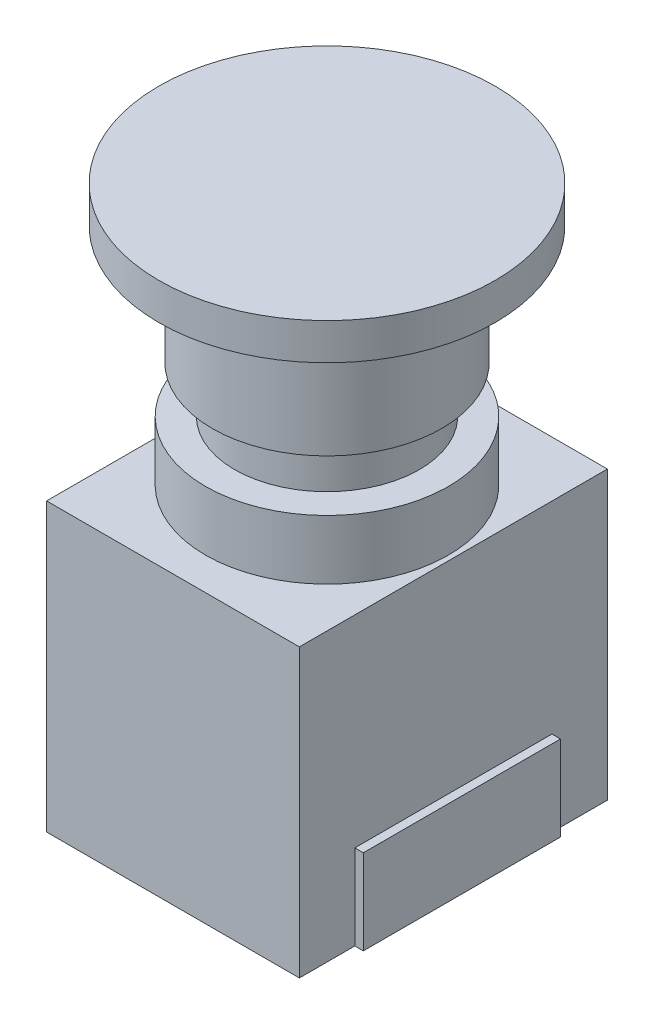
SolidWorks part; units mm, degrees
ref_plane "Front Plane" through (0, 0, 0) normal (0, 0, 1) x (1, 0, 0)
ref_plane "Top Plane" through (0, 0, 0) normal (0, 1, 0) x (1, 0, 0)
ref_plane "Right Plane" through (0, 0, 0) normal (1, 0, 0) x (0, 0, -1)
sketch "Sketch2" plane through (0, 0, 0) normal (0, 1, 0) x (1, 0, 0)
  line L1 (14.875, -18.125) -> (-14.875, -18.125)
  line L2 (14.875, -18.125) -> (14.875, 18.125)
  line L3 (14.875, 18.125) -> (-14.875, 18.125)
  line L4 (-14.875, -18.125) -> (-14.875, 18.125)
  line L5 (14.875, -18.125) -> (-14.875, 18.125) construction
  line L6 (14.875, 18.125) -> (-14.875, -18.125) construction
  point P0 (0, 0)
  dimension "D1" = 36.25
  dimension "D2" = 29.75
extrude "Boss-Extrude1" add sketch "Sketch2" along normal blind 33.75
sketch "Sketch3" plane through (0, 33.75, 0) normal (0, 1, 0) x (1, 0, 0)
  line L0 (-14.875, -18.125) -> (14.875, 18.125) construction
  circle A0 centre (0, 0) radius 14.3
  dimension "D1" = 28.6
extrude "Boss-Extrude2" add sketch "Sketch3" along normal blind 7
sketch "Sketch4" plane through (0, 40.75, 0) normal (0, 1, 0) x (1, 0, 0)
  circle A0 centre (0, 0) radius 10.875
  dimension "D1" = 21.75
extrude "Boss-Extrude3" add sketch "Sketch4" along normal blind 5.5
sketch "Sketch5" plane through (0, 46.25, 0) normal (0, 1, 0) x (1, 0, 0)
  circle A0 centre (0, 0) radius 13.5
  dimension "D1" = 27
extrude "Boss-Extrude4" add sketch "Sketch5" along normal blind 13.95
sketch "Sketch6" plane through (0, 60.2, 0) normal (0, 1, 0) x (1, 0, 0)
  circle A0 centre (0, 0) radius 19.8
  dimension "D1" = 39.6
extrude "Boss-Extrude5" add sketch "Sketch6" along normal blind 4.3
sketch "Sketch7" plane through (14.875, 0, 0) normal (1, 0, 0) x (0, 0, -1)
  line L1 (-11.6, 0) -> (11.6, 0)
  line L2 (-11.6, 0) -> (-11.6, 10)
  line L3 (-11.6, 10) -> (11.6, 10)
  line L4 (11.6, 0) -> (11.6, 10)
  point P4 (0, 0)
  dimension "D1" = 23.2
  dimension "D2" = 10
extrude "Boss-Extrude6" add sketch "Sketch7" along normal blind 1
